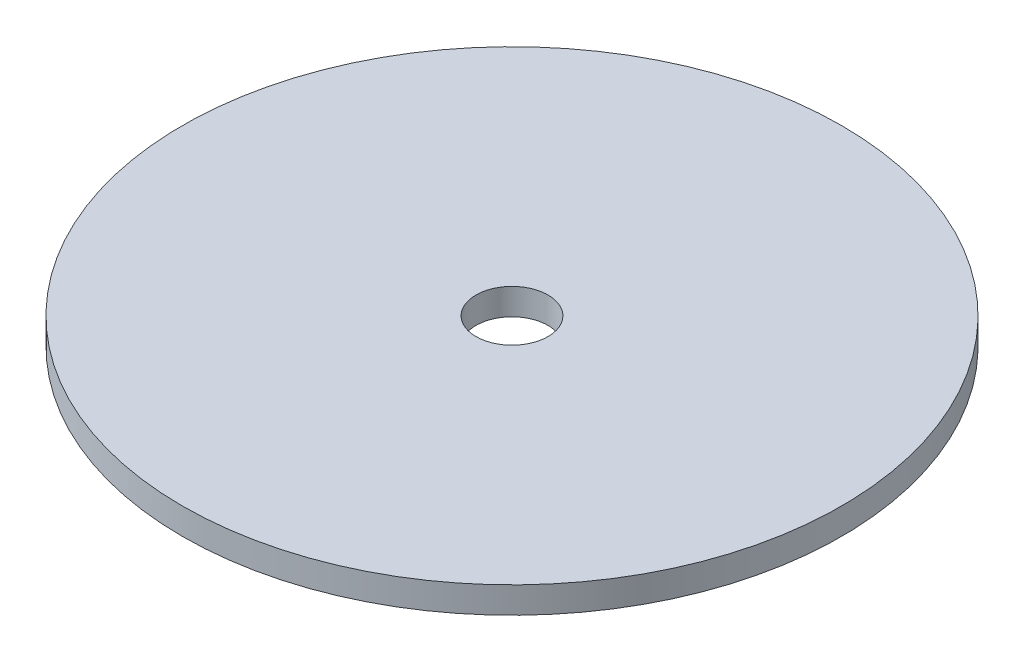
SolidWorks part; units mm, degrees
ref_plane "Front Plane" through (0, 0, 0) normal (0, 0, 1) x (1, 0, 0)
ref_plane "Top Plane" through (0, 0, 0) normal (0, 1, 0) x (1, 0, 0)
ref_plane "Right Plane" through (0, 0, 0) normal (1, 0, 0) x (0, 0, -1)
sketch "Sketch1" plane through (0, 0, 0) normal (0, 1, 0) x (1, 0, 0)
  circle A0 centre (0, 0) radius 37.5
  circle A1 centre (0, 0) radius 4.1
  dimension "D1" = 75
  dimension "D2" = 8.2
extrude "Boss-Extrude1" add sketch "Sketch1" along normal blind 3
